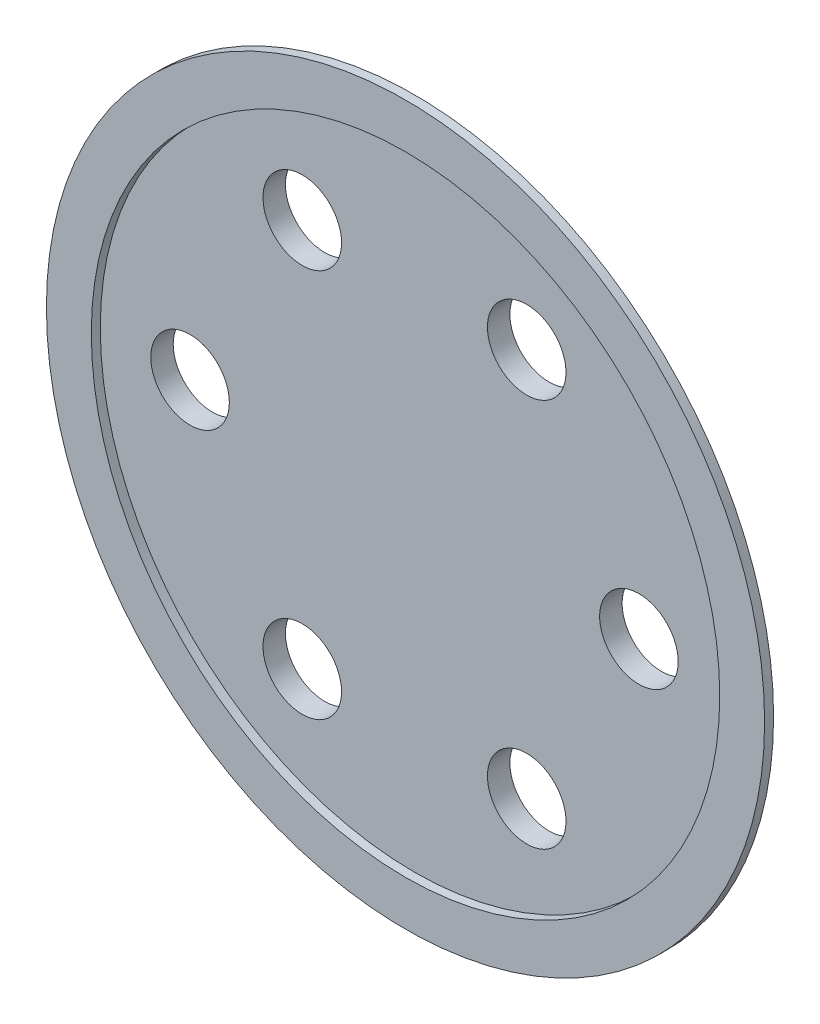
SolidWorks part; units mm, degrees
ref_plane "前视基准面" through (0, 0, 0) normal (0, 0, 1) x (1, 0, 0)
ref_plane "上视基准面" through (0, 0, 0) normal (0, 1, 0) x (1, 0, 0)
ref_plane "右视基准面" through (0, 0, 0) normal (1, 0, 0) x (0, 0, -1)
sketch "草图1" plane through (0, 0, 0) normal (0, 0, 1) x (1, 0, 0)
  circle A0 centre (0, 0) radius 15
  dimension "D1" = 30
extrude "拉伸-薄壁1" add sketch "草图1" along normal blind 0.4 thin thin type mid plane wall 2
sketch "草图2" plane through (0, 0, 0) normal (0, 0, -1) x (-1, 0, 0)
  circle A0 centre (0, 0) radius 14
  circle A1 centre (0, 0) radius 14 construction
extrude "凸台-拉伸1" add sketch "草图2" along normal blind 1
sketch "草图3" plane through (0, 0, 0) normal (0, 0, 1) x (1, 0, 0)
  circle A0 centre (10, 0) radius 1.75
  circle A1 centre (5, -8.6603) radius 1.75
  circle A2 centre (-5, -8.6603) radius 1.75
  circle A3 centre (-10, 0) radius 1.75
  circle A4 centre (-5, 8.6603) radius 1.75
  circle A5 centre (5, 8.6603) radius 1.75
  point P15 (0, 0)
  dimension "D1" = 3.5
  dimension "D2" = 10
  dimension "D3" = 6
extrude "切除-拉伸1" cut sketch "草图3" against normal up to surface (1 mm away) up to face at (-14, 0, -1)
scale "缩放比例1" bodies to scale 106 110 scale about origin uniform scaling yes scale factor 0.35
